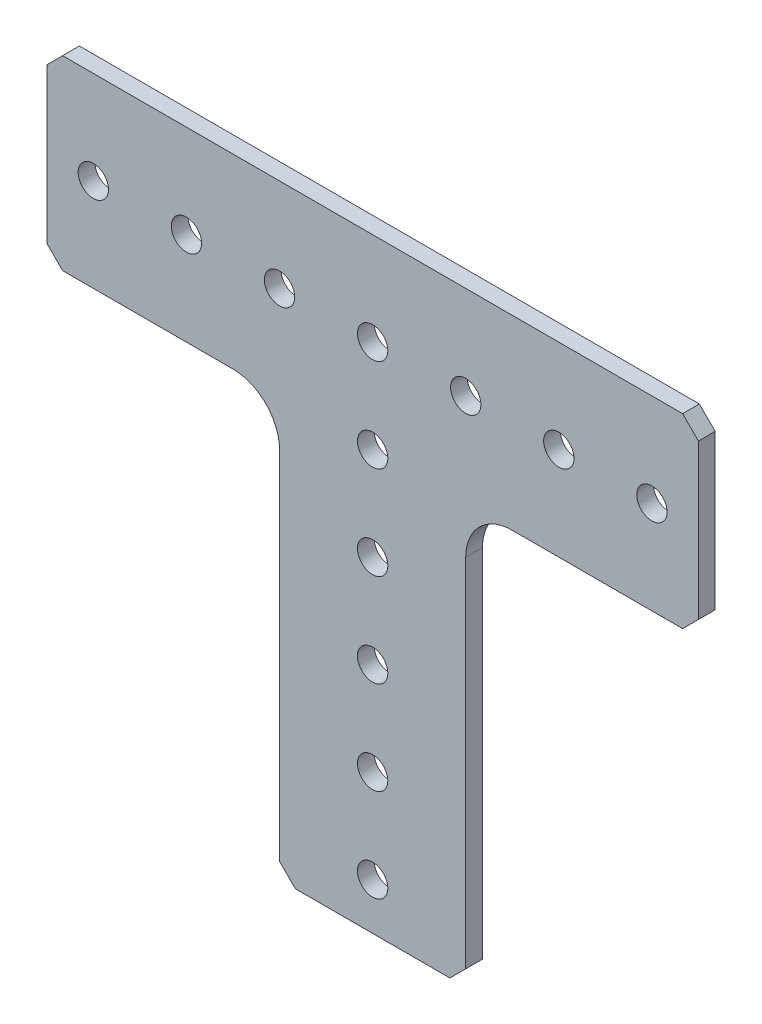
SolidWorks part; units mm, degrees
ref_plane "Front Plane" through (0, 0, 0) normal (0, 0, 1) x (1, 0, 0)
ref_plane "Top Plane" through (0, 0, 0) normal (0, 1, 0) x (1, 0, 0)
ref_plane "Right Plane" through (0, 0, 0) normal (1, 0, 0) x (0, 0, -1)
ref_plane "Plane1" through (0, 0, 2.286) normal (0, 0, 1) x (1, 0, 0)
sketch "Sketch1" plane through (0, 0, 2.286) normal (0, 0, 1) x (1, 0, 0)
  line L0 (12.7, -54.991) -> (12.7, -6.35)
  line L1 (19.05, 0) -> (42.291, 0)
  line L2 (42.291, 0) -> (44.45, 2.159)
  line L3 (44.45, 2.159) -> (44.45, 23.241)
  line L4 (44.45, 23.241) -> (42.291, 25.4)
  line L5 (42.291, 25.4) -> (-42.291, 25.4)
  line L6 (-42.291, 25.4) -> (-44.45, 23.241)
  line L7 (-44.45, 23.241) -> (-44.45, 2.159)
  line L8 (-44.45, 2.159) -> (-42.291, 0)
  line L9 (-42.291, 0) -> (-19.05, 0)
  line L10 (-12.7, -6.35) -> (-12.7, -54.991)
  line L11 (-12.7, -54.991) -> (-10.541, -57.15)
  line L12 (-10.541, -57.15) -> (10.541, -57.15)
  line L13 (10.541, -57.15) -> (12.7, -54.991)
  circle A0 centre (0, -38.1) radius 2.0701
  circle A1 centre (0, -12.7) radius 2.0701
  circle A2 centre (38.1, 12.7) radius 2.0701
  circle A3 centre (12.7, 12.7) radius 2.0701
  circle A4 centre (-12.7, 12.7) radius 2.0701
  circle A5 centre (-38.1, 12.7) radius 2.0701
  circle A6 centre (-25.4, 12.7) radius 2.0701
  circle A7 centre (0, 12.7) radius 2.0701
  circle A8 centre (25.4, 12.7) radius 2.0701
  circle A9 centre (0, 0) radius 2.0701
  circle A10 centre (0, -25.4) radius 2.0701
  circle A11 centre (0, -50.8) radius 2.0701
  arc A12 (12.7, -6.35) -> (19.05, 0) centre (19.05, -6.35) cw
  arc A13 (-19.05, 0) -> (-12.7, -6.35) centre (-19.05, -6.35) cw
extrude "Boss-Extrude1" add sketch "Sketch1" against normal blind 2.286
